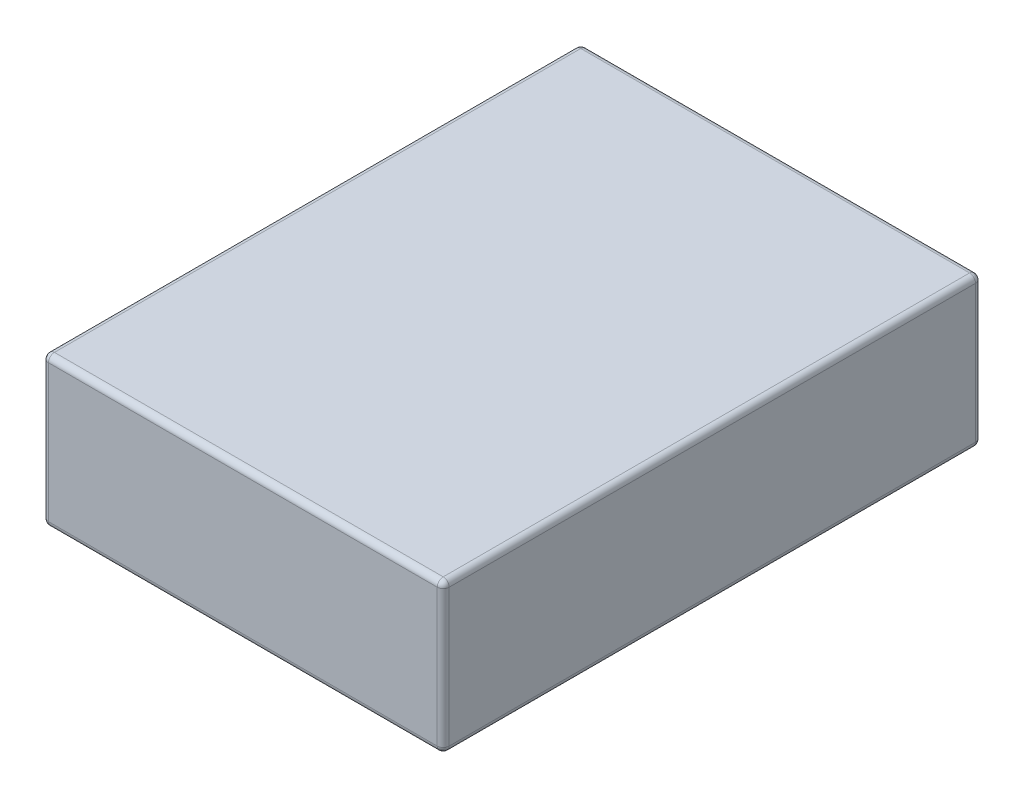
SolidWorks part; units mm, degrees
ref_plane "Front" through (0, 0, 0) normal (0, 0, 1) x (1, 0, 0)
ref_plane "Top" through (0, 0, 0) normal (0, 1, 0) x (1, 0, 0)
ref_plane "Right" through (0, 0, 0) normal (1, 0, 0) x (0, 0, -1)
sketch "Sketch1" plane through (0, 0, 0) normal (0, 1, 0) x (1, 0, 0)
  line L1 (-33.5, -45) -> (33.5, -45)
  line L2 (-33.5, -45) -> (-33.5, 45)
  line L3 (-33.5, 45) -> (33.5, 45)
  line L4 (33.5, -45) -> (33.5, 45)
  line L5 (-33.5, -45) -> (33.5, 45) construction
  line L6 (-33.5, 45) -> (33.5, -45) construction
  point P0 (0, 0)
  dimension "D1" = 67
  dimension "D2" = 90
extrude "Boss-Extrude1" add sketch "Sketch1" along normal blind 25
fillet "Fillet1" radius 1 12 edges at (-33.5, 0, 0) (0, 0, -45) (33.5, 12.5, -45) (-33.5, 12.5, 45) (33.5, 25, 0) (0, 25, 45) (-33.5, 12.5, -45) (33.5, 12.5, 45) (-33.5, 25, 0) (0, 25, -45) (0, 0, 45) (33.5, 0, 0)
